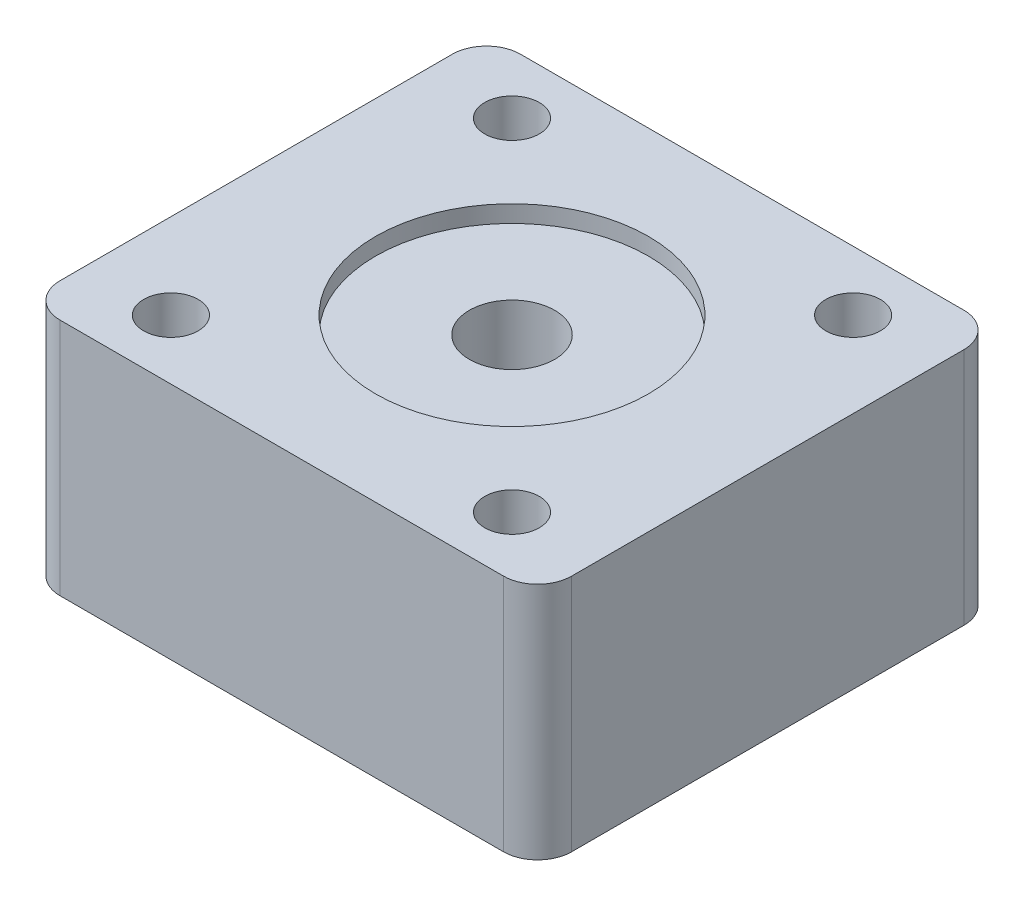
SolidWorks part; units mm, degrees
material "6061 合金"
ref_plane "前视基准面" through (0, 0, 0) normal (0, 0, 1) x (1, 0, 0)
ref_plane "上视基准面" through (0, 0, 0) normal (0, 1, 0) x (1, 0, 0)
ref_plane "右视基准面" through (0, 0, 0) normal (1, 0, 0) x (0, 0, -1)
sketch "草图1" plane through (0, 0, 0) normal (0, 1, 0) x (1, 0, 0)
  line L1 (-10, 10) -> (10, 10) construction
  line L2 (-10, 10) -> (-10, -10) construction
  line L3 (-10, -10) -> (10, -10) construction
  line L4 (10, 10) -> (10, -10) construction
  line L5 (-10, 10) -> (10, -10) construction
  line L6 (-10, -10) -> (10, 10) construction
  line L7 (-15, 13.5) -> (15, 13.5)
  line L8 (-15, 13.5) -> (-15, -13.5)
  line L9 (-15, -13.5) -> (15, -13.5)
  line L10 (15, 13.5) -> (15, -13.5)
  line L11 (-15, 13.5) -> (15, -13.5) construction
  line L12 (-15, -13.5) -> (15, 13.5) construction
  circle A0 centre (-10, 10) radius 1.6
  circle A1 centre (10, 10) radius 1.6
  circle A2 centre (10, -10) radius 1.6
  circle A3 centre (-10, -10) radius 1.6
  point P0 (0, 0)
  point P3 (0, 0)
  point P16 (0, 0)
  dimension "D2" = 3.2
  dimension "D4" = 30
  dimension "D5" = 27
  dimension "D3" = 20
  dimension "D1" = 4
extrude "凸台-拉伸1" add sketch "草图1" along normal blind 14
sketch "草图2" plane through (0, 14, 0) normal (0, 1, 0) x (1, 0, 0)
  circle A0 centre (0, 0) radius 2.5
  dimension "D1" = 5
extrude "切除-拉伸1" cut sketch "草图2" against normal through all
cosmetic thread "装饰螺纹线1" parameters "D2"=6
sketch "草图3" plane through (0, 14, 0) normal (0, 1, 0) x (1, 0, 0)
  circle A0 centre (0, 0) radius 8
  dimension "D1" = 16
extrude "切除-拉伸2" cut sketch "草图3" against normal blind 1
fillet "圆角1" radius 2 4 edges at (-15, 7, 13.5) (-15, 7, -13.5) (15, 7, -13.5) (15, 7, 13.5)
